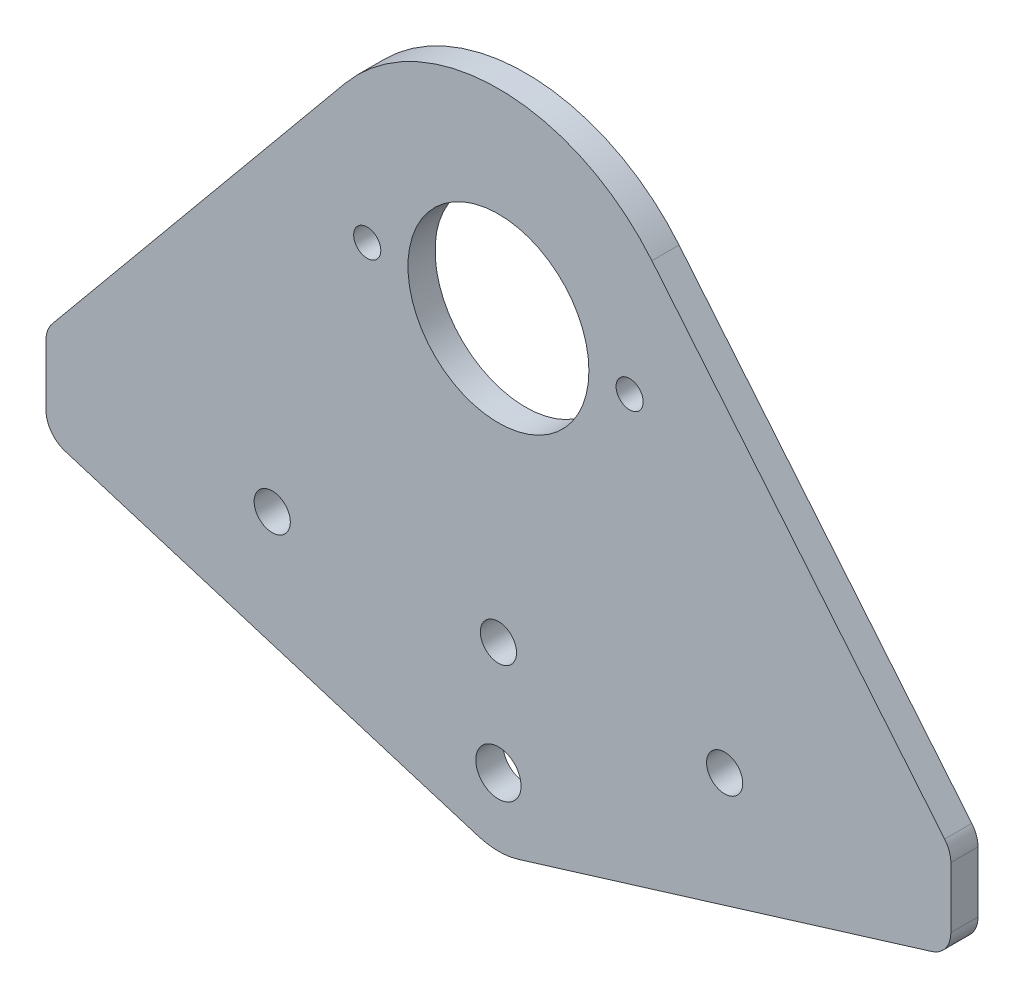
SolidWorks part; units mm, degrees
material "AISI 1020"
ref_plane "Front Plane" through (0, 0, 0) normal (0, 0, 1) x (1, 0, 0)
ref_plane "Top Plane" through (0, 0, 0) normal (0, 1, 0) x (1, 0, 0)
ref_plane "Right Plane" through (0, 0, 0) normal (1, 0, 0) x (0, 0, -1)
sketch "Sketch1" plane through (0, 0, 0) normal (0, 0, 1) x (1, 0, 0)
  line L0 (-50, -36) -> (50, -36) construction
  line L1 (-50, -36) -> (-50, -26)
  line L2 (-50, -26) -> (50, -26) construction
  line L3 (50, -26) -> (50, -36)
  line L4 (0, -26) -> (0, -36) construction
  line L5 (-50, -31) -> (50, -31) construction
  line L6 (-50, -26) -> (-16.9641, 14.0079)
  line L7 (50, -26) -> (16.9641, 14.0079)
  line L8 (50, -36) -> (2.2005, -50.6699)
  line L9 (-50, -36) -> (-2.2005, -50.6699)
  circle A0 centre (0, 0) radius 22
  circle A1 centre (0, -31) radius 2
  circle A2 centre (-25, -31) radius 2
  circle A3 centre (25, -31) radius 2
  circle A4 centre (0, 0) radius 14.5 construction
  circle A5 centre (-14.5, 0) radius 1.5
  circle A6 centre (14.5, 0) radius 1.5
  circle A7 centre (0, 0) radius 10
  circle A8 centre (0, -43.5) radius 7.5
  circle A9 centre (0, -43.5) radius 2.5
  point P5 (0, -36)
  point P29 (0, 0)
  point P32 (0, -44.9712)
  dimension "D1" = 44
  dimension "D3" = 4
  dimension "D7" = 3
  dimension "D8" = 20
  dimension "D10" = 15
  dimension "D11" = 5
  dimension "D2" = 10
  dimension "D4" = 25
  dimension "D5" = 26
  dimension "D6" = 100
  dimension "D9" = 29
extrude "Boss-Extrude1" add sketch "Sketch1" along normal blind 3 contours A0 L6 L1 L0 L3 L7 A1 A2 A3 | A0 A7 A5 A6 | A8 A9
fillet "Fillet1" radius 3 4 edges at (-50, -26, 1.5) (50, -26, 1.5) (50, -36, 1.5) (-50, -36, 1.5)
